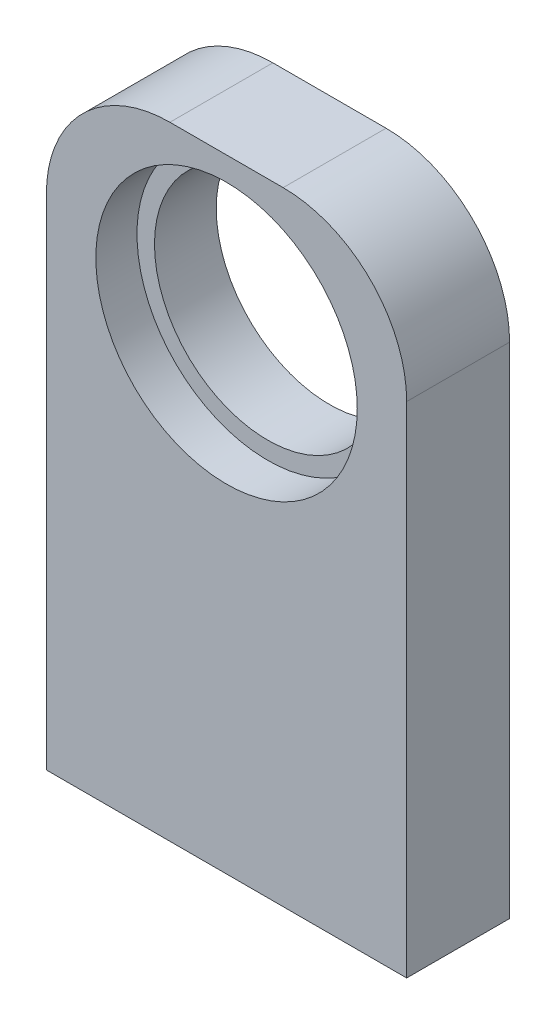
SolidWorks part; units mm, degrees
ref_plane "Front Plane" through (0, 0, 0) normal (0, 0, 1) x (1, 0, 0)
ref_plane "Top Plane" through (0, 0, 0) normal (0, 1, 0) x (1, 0, 0)
ref_plane "Right Plane" through (0, 0, 0) normal (1, 0, 0) x (0, 0, -1)
sketch "Sketch1" plane through (0, 0, 0) normal (0, 1, 0) x (1, 0, 0)
  line L1 (-16.3353, 5) -> (18.6647, 5)
  line L2 (-16.3353, 5) -> (-16.3353, -5)
  line L3 (-16.3353, -5) -> (18.6647, -5)
  line L4 (18.6647, 5) -> (18.6647, -5)
  dimension "D1" = 35
  dimension "D2" = 10
  dimension "D3" = 5
extrude "Boss-Extrude1" add sketch "Sketch1" along normal blind 60.5
sketch "Sketch2" plane through (0, 0, 5) normal (0, 0, 1) x (1, 0, 0)
  line L0 (18.6647, 60.5) -> (18.6647, 0) construction
  line L2 (-16.3353, 60.5) -> (18.6647, 60.5) construction
  circle A0 centre (1.1647, 45.5) radius 11
  dimension "D1" = 17.5
  dimension "D2" = 15
extrude "Cut-Extrude1" cut sketch "Sketch2" against normal through all
sketch "Sketch3" plane through (0, 0, 0) normal (0, -1, 0) x (1, 0, 0)
  line L0 (18.6647, -5) -> (-16.3353, -5) construction
  line L1 (-16.3353, -5) -> (-16.3353, 5) construction
  line L2 (18.6647, 5) -> (18.6647, -5) construction
  circle A0 centre (-8.3353, 0) radius 1.75
  circle A1 centre (10.6647, 0) radius 1.75
  point P4 (-16.3353, 0)
  dimension "D1" = 5
  dimension "D3" = 5
  dimension "D2" = 8
  dimension "D4" = 8
extrude "Cut-Extrude2" cut sketch "Sketch3" against normal blind 10
fillet "Fillet1" radius 12 2 edges at (18.6647, 60.5, 0) (-16.3353, 60.5, 0)
sketch "Sketch4" plane through (0, 0, 5) normal (0, 0, 1) x (1, 0, 0)
  circle A0 centre (1.1647, 45.5) radius 12.7
extrude "Cut-Extrude3" cut sketch "Sketch4" against normal blind 4
